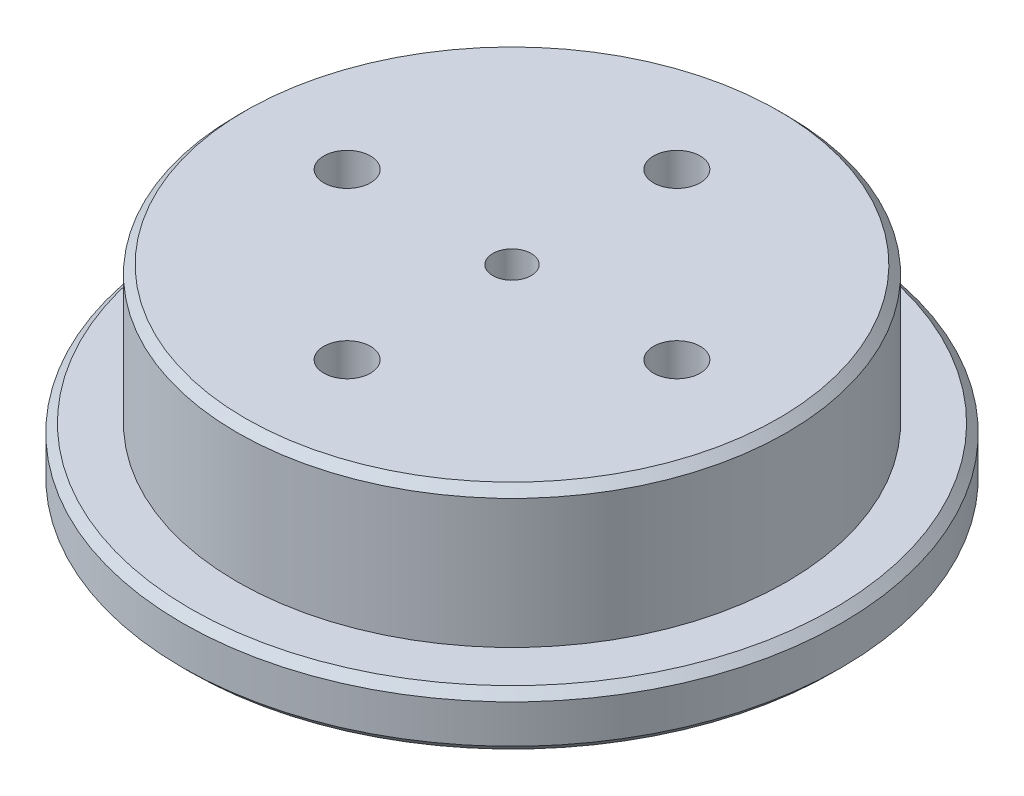
SolidWorks part; units mm, degrees
ref_plane "Спереди" through (0, 0, 0) normal (0, 0, 1) x (1, 0, 0)
ref_plane "Сверху" through (0, 0, 0) normal (0, 1, 0) x (1, 0, 0)
ref_plane "Справа" through (0, 0, 0) normal (1, 0, 0) x (0, 0, -1)
sketch "Эскиз1" plane through (0, 0, 0) normal (0, 1, 0) x (1, 0, 0)
  circle A0 centre (0, 0) radius 120
extrude "Бобышка-Вытянуть1" add sketch "Эскиз1" along normal blind 20
sketch "Эскиз2" plane through (0, 20, 0) normal (0, 1, 0) x (1, 0, 0)
  circle A0 centre (0, 0) radius 100
extrude "Бобышка-Вытянуть2" add sketch "Эскиз2" along normal blind 50
sketch "Эскиз3" plane through (0, 70, 0) normal (0, 1, 0) x (1, 0, 0)
  line L0 (0, 72.4779) -> (0, -78.3645) construction
  line L1 (-77.2608, 0) -> (72.11, 0) construction
  circle A0 centre (0, 0) radius 60 construction
  circle A2 centre (0, 60) radius 8.5
  circle A3 centre (60, 0) radius 8.5
  circle A4 centre (0, -60) radius 8.5
  circle A5 centre (-60, 0) radius 8.5
  point P18 (0, 0)
  dimension "D1" = 120
  dimension "D2" = 17
  dimension "D3" = 4
extrude "Вырез-Вытянуть1" cut sketch "Эскиз3" against normal blind 80
sketch "Эскиз4" plane through (0, 0, 0) normal (0, -1, 0) x (1, 0, 0)
  circle A0 centre (0, 0) radius 20
  dimension "D1" = 40
extrude "Бобышка-Вытянуть3" add sketch "Эскиз4" along normal blind 20
sketch "Эскиз5" plane through (0, 70, 0) normal (0, 1, 0) x (1, 0, 0)
  circle A0 centre (0, 0) radius 8.5698
hole_wizard "Отверстие обработанное метчиком M161" positions "Эскиз12" profile "Эскиз10" tap size "M16" standard "ISO"
sketch "Эскиз12" plane through (0, 70, 0) normal (0, 1, 0) x (1, 0, 0)
  point P0 (0, 0)
cosmetic thread "Отверстие резьбы1" parameters "D1"=15, "D2"=16
sketch "Эскиз10" plane through (0, 70, 0) normal (1, 0, 0) x (0, 0, 1)
  line L0 (0, 0) -> (0, 24.206)
  line L1 (0, 24.206) -> (7, 20)
  line L2 (7, 20) -> (7, 0)
  line L5 (7, 0) -> (0, 0)
  line L10 (0, 24.206) -> (-7, 20) construction
  line L11 (0, -6.35) -> (0, 107.95) construction
  dimension "Диаметр сверла" = 14
  dimension "Глубина сверла" = 20
  dimension "Угол заточки сверла" = 118
chamfer "Фаска1" distance 3 angle 45 3 edges at (0, 0, 120) (0, 20, 120) (0, 70, 100)
chamfer "Фаска2" distance 3 angle 45 1 edges at (0, -20, -20)
